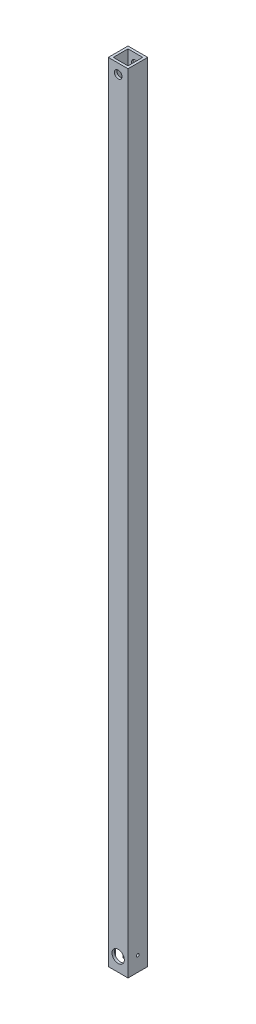
SolidWorks part; units mm, degrees
material "1060 Alloy"
ref_plane "Front Plane" through (0, 0, 0) normal (0, 0, 1) x (1, 0, 0)
ref_plane "Top Plane" through (0, 0, 0) normal (0, 1, 0) x (1, 0, 0)
ref_plane "Right Plane" through (0, 0, 0) normal (1, 0, 0) x (0, 0, -1)
sketch "Sketch1" plane through (0, 0, 0) normal (0, 1, 0) x (1, 0, 0)
  line L1 (-6.35, 6.35) -> (6.35, 6.35)
  line L2 (-6.35, 6.35) -> (-6.35, -6.35)
  line L3 (-6.35, -6.35) -> (6.35, -6.35)
  line L4 (6.35, 6.35) -> (6.35, -6.35)
  line L5 (-6.35, 6.35) -> (6.35, -6.35) construction
  line L6 (-6.35, -6.35) -> (6.35, 6.35) construction
  point P0 (0, 0)
  dimension "D1" = 12.7
extrude "Extrude-Thin1" add sketch "Sketch1" along normal blind 508 thin
sketch "Sketch2" plane through (0, 0, 6.35) normal (0, 0, 1) x (1, 0, 0)
  line L0 (-6.35, 0) -> (6.35, 0) construction
  line L1 (-6.35, 508) -> (-6.35, 0) construction
  circle A1 centre (0, 8.9123) radius 3.9688
  dimension "D3" = 7.9375
  dimension "D1" = 8.9123
  dimension "D2" = 6.35
extrude "Cut-Extrude1" cut sketch "Sketch2" against normal up to surface (1.5875 mm away) up to face at (0, 254, 4.7625)
sketch "Sketch3" plane through (0, 0, 6.35) normal (0, 0, 1) x (1, 0, 0)
  line L0 (-6.35, 508) -> (6.35, 508) construction
  line L1 (6.35, 508) -> (6.35, 0) construction
  circle A0 centre (0, 501.65) radius 2.4765
  dimension "D1" = 4.953
  dimension "D2" = 6.35
  dimension "D3" = 6.35
extrude "Cut-Extrude2" cut sketch "Sketch3" against normal through all and the other way through all
sketch "Sketch4" plane through (6.35, 0, 0) normal (1, 0, 0) x (0, 0, -1)
  line L0 (-6.35, 0) -> (6.35, 0) construction
  circle A0 centre (0, 9.525) radius 0.889
  point P4 (0, 0)
  dimension "D1" = 1.778
  dimension "D2" = 9.525
extrude "Cut-Extrude3" cut sketch "Sketch4" against normal up to next contours A0
sketch "Sketch5" plane through (-6.35, 0, 0) normal (-1, 0, 0) x (0, 0, 1)
  line L0 (-6.35, 0) -> (6.35, 0) construction
  line L1 (-3.175, 0) -> (3.175, 0)
  line L2 (-3.175, 0) -> (-3.175, 9.525)
  line L3 (-3.175, 9.525) -> (3.175, 9.525)
  line L4 (3.175, 0) -> (3.175, 9.525)
  line L5 (-6.35, 508) -> (-6.35, 0) construction
  dimension "D1" = 6.35
  dimension "D2" = 9.525
  dimension "D3" = 3.175
extrude "Cut-Extrude4" cut sketch "Sketch5" against normal up to next
